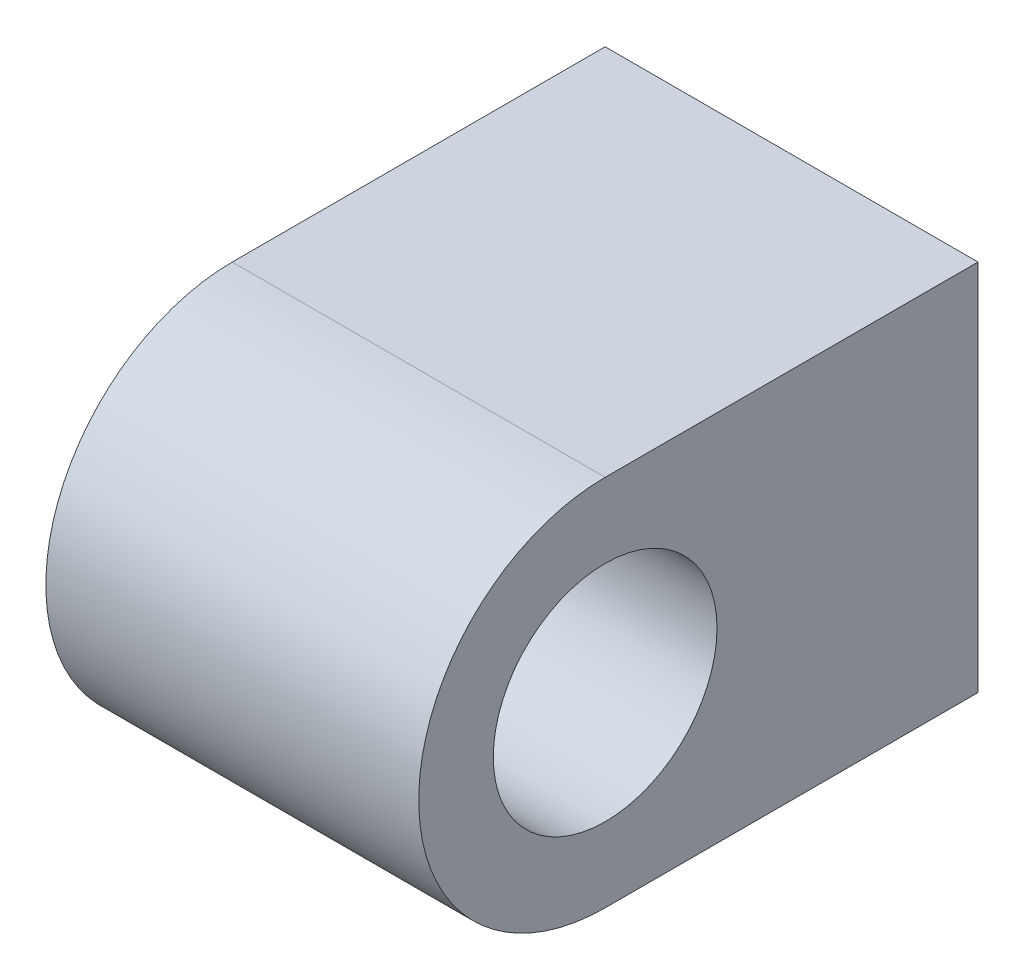
SolidWorks part; units mm, degrees
ref_plane "Plan de face" through (0, 0, 0) normal (0, 0, 1) x (1, 0, 0)
ref_plane "Plan de dessus" through (0, 0, 0) normal (0, 1, 0) x (1, 0, 0)
ref_plane "Plan de droite" through (0, 0, 0) normal (1, 0, 0) x (0, 0, -1)
ref_plane "Plan1" through (0, 0, 0) normal (-1, 0, 0) x (0, -1, 0)
sketch "Esquisse1" plane through (0, 0, 0) normal (-1, 0, 0) x (0, -1, 0)
  line L0 (-5, 5) -> (-5, 0)
  line L1 (-5, 0) -> (0, 0)
  line L2 (0, 0) -> (0, 5)
  circle A0 centre (-2.5, 5) radius 1.5
  arc A1 (0, 5) -> (-5, 5) centre (-2.5, 5) ccw
extrude "Boss.-Extru.1" add sketch "Esquisse1" against normal blind 5
